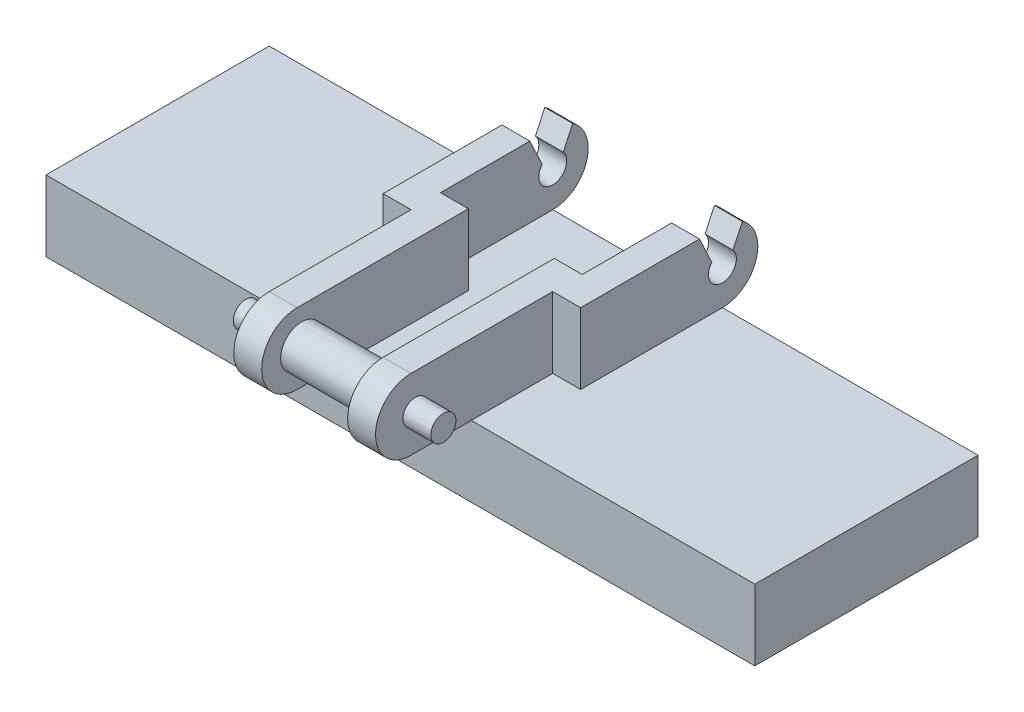
SolidWorks part; units mm, degrees
ref_plane "Front Plane" through (0, 0, 0) normal (0, 0, 1) x (1, 0, 0)
ref_plane "Top Plane" through (0, 0, 0) normal (0, 1, 0) x (1, 0, 0)
ref_plane "Right Plane" through (0, 0, 0) normal (1, 0, 0) x (0, 0, -1)
sketch "Sketch1" plane through (0, 0, 0) normal (0, 1, 0) x (1, 0, 0)
  line L0 (-12.7, 0) -> (12.7, 0) construction
  line L1 (-12.7, 2.54) -> (12.7, 2.54)
  line L2 (-12.7, 2.54) -> (-12.7, -2.54)
  line L3 (-12.7, -2.54) -> (12.7, -2.54)
  line L4 (12.7, 2.54) -> (12.7, -2.54)
  line L6 (0, 2.54) -> (0, -2.54) construction
  dimension "D1" = 25.4
  dimension "D2" = 5.08
extrude "Boss-Extrude1" add sketch "Sketch1" along normal blind 2.54
sketch "Sketch5" plane through (0, 2.54, 0) normal (0, 1, 0) x (1, 0, 0)
  line L0 (-3.54, 2.54) -> (-3.54, -2.54)
  line L1 (12.7, 2.54) -> (-12.7, 2.54) construction
  line L2 (-3.54, -2.54) -> (-2.54, -2.54)
  line L3 (-2.54, -2.54) -> (-2.54, -7.62)
  line L4 (-2.54, -7.62) -> (-1.54, -7.62)
  line L5 (-1.54, -7.62) -> (-1.54, -1.4827)
  line L6 (-1.54, -1.4827) -> (-2.54, -1.4827)
  line L7 (-2.54, -1.4827) -> (-2.54, 2.54)
  line L8 (-2.54, 2.54) -> (-3.54, 2.54)
  line L9 (0, 2.54) -> (0, -2.54) construction
  line L10 (-12.7, -2.54) -> (12.7, -2.54) construction
  dimension "D5" = 6.1373
  dimension "D1" = 1
  dimension "D2" = 1
  dimension "D3" = 5.08
  dimension "D4" = 1
  dimension "D6" = 2.54
extrude "Boss-Extrude5" add sketch "Sketch5" along normal blind 2.54
sketch "Sketch6" plane through (-1.54, 0, 0) normal (1, 0, 0) x (0, 0, -1)
  line L1 (-7.62, 5.08) -> (-7.62, 2.54) construction
  line L2 (-7.62, 2.54) -> (-7.62, 5.08) construction
  circle A1 centre (-7.62, 3.81) radius 1.27
extrude "Boss-Extrude6" add sketch "Sketch6" against normal up to surface (1 mm away) up to face at (-2.54, 3.81, 5.08)
sketch "Sketch7" plane through (-2.54, 0, 0) normal (1, 0, 0) x (0, 0, -1)
  line L0 (2.54, 5.08) -> (2.54, 2.54) construction
  line L1 (-1.4827, 5.08) -> (2.54, 5.08) construction
  line L2 (2.54, 5.08) -> (2.54, 2.54)
  arc A0 (2.54, 5.08) -> (2.54, 2.54) centre (2.54, 3.81) cw
extrude "Boss-Extrude7" add sketch "Sketch7" against normal up to surface (1 mm away) contours A0 L2 up to face at (-3.54, 3.81, 0)
mirror "Mirror1" about plane through (0, 0, 0) normal (1, 0, 0) of "Boss-Extrude7", "Boss-Extrude6", "Boss-Extrude5"
sketch "Sketch8" plane through (0, 2.54, 0) normal (0, -1, 0) x (1, 0, 0)
  line L0 (0, 2.54) -> (0, -2.54) construction
  line L1 (12.7, -2.54) -> (-12.7, -2.54)
  line L2 (12.7, -2.54) -> (12.7, 5.46)
  line L3 (12.7, 5.46) -> (-12.7, 5.46)
  line L4 (-12.7, -2.54) -> (-12.7, 5.46)
  line L5 (-12.7, 2.54) -> (12.7, 2.54) construction
  line L6 (12.7, -2.54) -> (-12.7, -2.54) construction
  line L7 (12.7, 2.54) -> (12.7, -2.54) construction
  line L8 (-12.7, -2.54) -> (-12.7, 2.54) construction
  dimension "D1" = 8
extrude "Boss-Extrude8" add sketch "Sketch8" along normal blind 2.54
sketch "Sketch11" plane through (3.54, 0, 0) normal (1, 0, 0) x (0, 0, -1)
  circle A0 centre (2.54, 3.81) radius 0.5
  arc A1 (2.54, 2.54) -> (2.54, 5.08) centre (2.54, 3.81) ccw construction
  dimension "D1" = 1
extrude "Cut-Extrude1" cut sketch "Sketch11" against normal through all
sketch "Sketch12" plane through (3.54, 0, 0) normal (1, 0, 0) x (0, 0, -1)
  line L1 (2.54, 5.08) -> (-2.54, 5.08) construction
  line L4 (1.9238, 5.08) -> (1.7203, 5.08)
  line L6 (1.7203, 5.08) -> (2.1779, 4.1011)
  line L7 (2.54, 3.3454) -> (2.54, 5.08) construction
  line L8 (1.9238, 5.08) -> (2.54, 5.08)
  line L9 (3.2563, 4.8587) -> (2.9021, 4.1011)
  arc A0 (2.54, 5.08) -> (3.2563, 4.8587) centre (2.54, 3.81) cw
  arc A2 (2.1779, 4.1011) -> (2.9021, 4.1011) centre (2.54, 3.81) ccw
  dimension "D2" = 0.4646
  dimension "D1" = 0.9789
  dimension "D3" = 0.7576
extrude "Cut-Extrude2" cut sketch "Sketch12" against normal blind 10.54
sketch "Sketch2" plane through (0, 2.54, 0) normal (0, 1, 0) x (1, 0, 0)
  line L1 (-3.54, 1.92) -> (-2.54, 1.92)
  line L2 (-3.54, 1.92) -> (-3.54, -2.54)
  line L3 (-3.54, -2.54) -> (-2.54, -2.54)
  line L4 (-2.54, 1.92) -> (-2.54, -2.54)
  line L5 (-12.7, -2.54) -> (12.7, -2.54) construction
  line L7 (3.54, -2.54) -> (2.54, -2.54)
  line L8 (3.54, 1.92) -> (2.54, 1.92)
  line L9 (3.54, 1.92) -> (3.54, -2.54)
  line L10 (2.54, 1.92) -> (2.54, -2.54)
  dimension "D1" = 1
  dimension "D2" = 4.46
  dimension "D3" = 4.46
  dimension "D4" = 1
extrude "Boss-Extrude2" add sketch "Sketch2" along normal blind 2.54
sketch "Sketch4" [suppressed] plane through (3.54, 0, 0) normal (1, 0, 0) x (0, 0, -1)
  line L1 (-2.54, 5.08) -> (-2.54, 2.54) construction
  circle A0 centre (-2.54, 3.81) radius 1.27
extrude "Boss-Extrude4" [suppressed] add sketch "Sketch4" against normal up to surface (1 mm away)
sketch "Sketch13" plane through (1.54, 0, 0) normal (-1, 0, 0) x (0, 0, 1)
  line L1 (7.46, 4.56) -> (7.46, 2.54) construction
  line L2 (7.62, 2.54) -> (5.46, 2.54) construction
  circle A5 centre (7.46, 3.81) radius 0.75
  dimension "D1" = 1.5
extrude "Boss-Extrude12" add sketch "Sketch13" along normal up to surface (3.08 mm away) up to face at (-1.54, 3.556, 4.9871)
sketch "Sketch14" plane through (3.54, 0, 0) normal (1, 0, 0) x (0, 0, -1)
  line L0 (1.92, 4.6528) -> (1.7203, 5.08)
  line L1 (1.92, 4.6528) -> (2.1614, 4.1366) construction
  line L2 (1.92, 5.08) -> (-2.54, 5.08) construction
  line L3 (1.7203, 5.08) -> (1.92, 5.08)
  line L4 (1.92, 5.08) -> (1.92, 4.6528)
extrude "Cut-Extrude3" cut sketch "Sketch14" against normal blind 9 contours L0 L3 L4
sketch "Sketch16" plane through (-2.54, 0, 0) normal (-1, 0, 0) x (0, 0, 1)
  circle A0 centre (7.46, 3.81) radius 0.45
  circle A1 centre (7.46, 3.81) radius 0.75 construction
  dimension "D1" = 0.9
extrude "Boss-Extrude13" add sketch "Sketch16" along normal up to surface and the other way up to surface up to face at (-3.54, 3.8973, -1.196) other way up to face at (3.54, 3.8973, -1.196)
